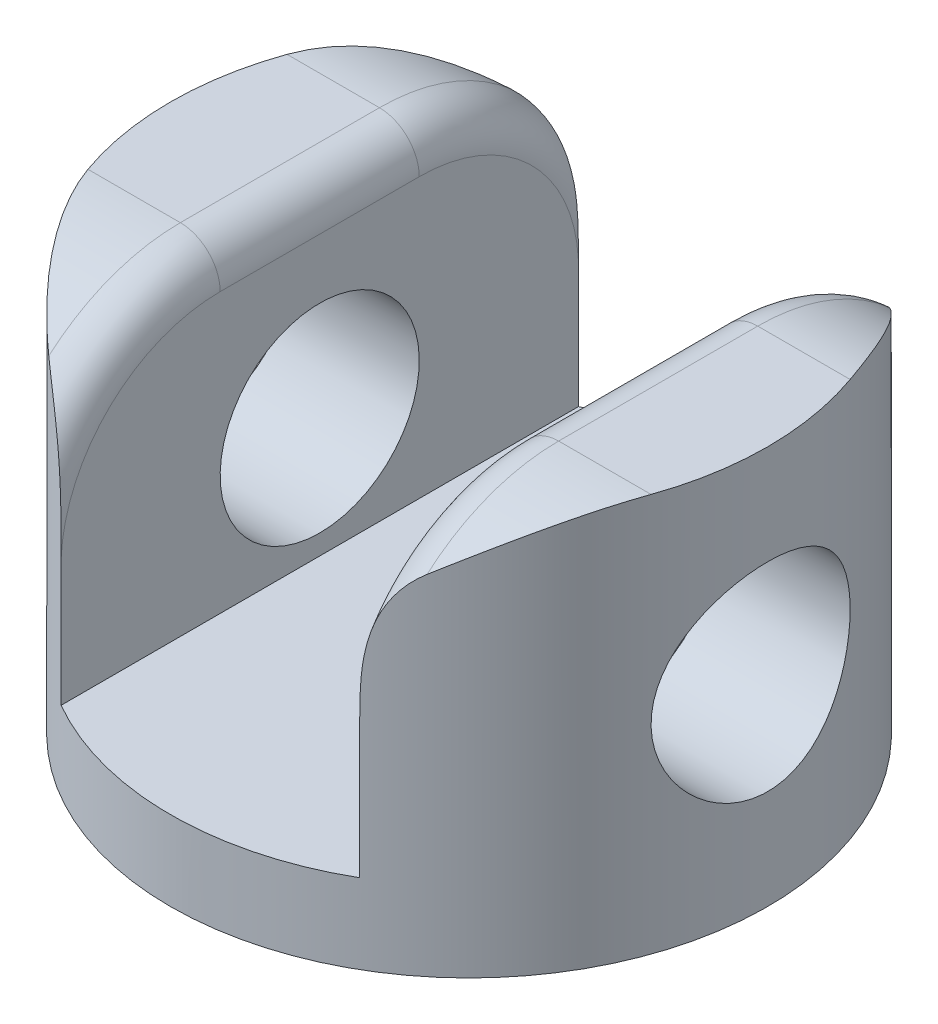
SolidWorks part; units mm, degrees
ref_plane "Front Plane" through (0, 0, 0) normal (0, 0, 1) x (1, 0, 0)
ref_plane "Top Plane" through (0, 0, 0) normal (0, 1, 0) x (1, 0, 0)
ref_plane "Right Plane" through (0, 0, 0) normal (1, 0, 0) x (0, 0, -1)
sketch "Sketch1" plane through (0, 0, 0) normal (0, 1, 0) x (1, 0, 0)
  circle A0 centre (0, 0) radius 15
  dimension "D1" = 30
extrude "Boss-Extrude1" add sketch "Sketch1" along normal blind 20
sketch "Sketch2" plane through (0, 0, 0) normal (1, 0, 0) x (0, 0, -1)
  line L1 (15, 20) -> (-15, 20) construction
  line L3 (0, 0) -> (0, 20) construction
  line L4 (5, 20) -> (-5, 20)
  line L6 (-15, 10) -> (-15, 20)
  line L7 (-15, 20) -> (15, 20)
  line L8 (15, 20) -> (15, 10)
  arc A0 (15, 10) -> (5, 20) centre (5, 10) ccw
  arc A1 (-5, 20) -> (-15, 10) centre (-5, 10) ccw
  circle A2 centre (0, 10) radius 5
  dimension "D1" = 10
  dimension "D2" = 10
extrude "Cut-Extrude1" cut sketch "Sketch2" against normal through all both and the other way through all contours A1 L7 L6 | A0 L8 L7 | A2
sketch "Sketch3" plane through (0, 0, 0) normal (0, 0, 1) x (1, 0, 0)
  line L0 (0, 20) -> (0, 0) construction
  line L1 (-14.1421, 20) -> (14.1421, 20) construction
  line L3 (-7.5, 20) -> (7.5, 20)
  line L4 (-7.5, 20) -> (-7.5, 4)
  line L5 (-7.5, 4) -> (7.5, 4)
  line L6 (7.5, 20) -> (7.5, 4)
  point P9 (0, 20)
  dimension "D1" = 15
  dimension "D2" = 16
extrude "Cut-Extrude2" cut sketch "Sketch3" against normal through all both and the other way through all
fillet "Fillet1" radius 2 6 edges at (7.5, 20, 0) (-7.5, 20, 0) (7.5, 18.9478, -9.465) (7.5, 18.9478, 9.465) (-7.5, 18.9478, -9.465) (-7.5, 18.9478, 9.465)
